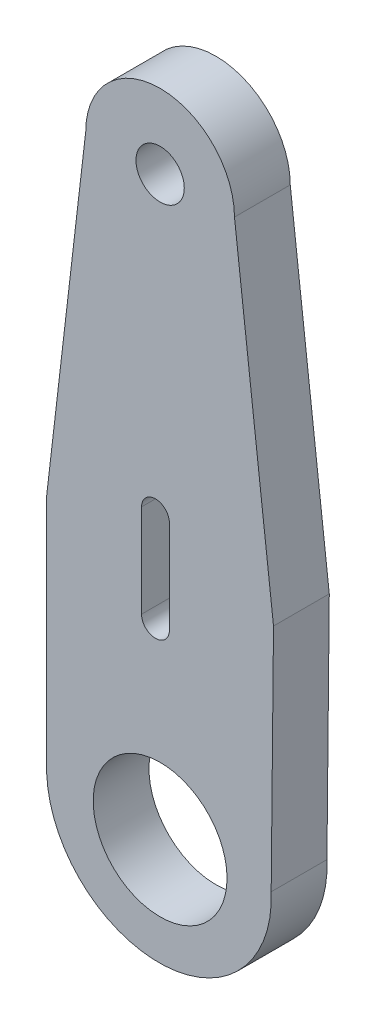
SolidWorks part; units mm, degrees
ref_plane "Front Plane" through (0, 0, 0) normal (0, 0, 1) x (1, 0, 0)
ref_plane "Top Plane" through (0, 0, 0) normal (0, 1, 0) x (1, 0, 0)
ref_plane "Right Plane" through (0, 0, 0) normal (1, 0, 0) x (0, 0, -1)
sketch "Model" plane through (0, 0, 0) normal (0, 0, 1) x (1, 0, 0)
  line L0 (54.4, 32.325) -> (54.4, 38.325)
  line L1 (66.6, 38.325) -> (66.4744, 25.8791)
  line L2 (64.5, 56.3249) -> (66.6, 38.325)
  line L3 (56.5, 56.3249) -> (54.4, 38.325)
  line L4 (59.5, 35.3249) -> (59.5, 40.3249)
  line L5 (61, 40.3249) -> (61, 35.3249)
  line L6 (54.4, 32.325) -> (54.4, 25.325)
  circle A0 centre (60.5, 56.3249) radius 1.3
  circle A1 centre (60.5001, 25.325) radius 3.6
  arc A2 (59.5, 40.3249) -> (61, 40.3249) centre (60.25, 40.3249) cw
  arc A3 (59.5, 35.3249) -> (61, 35.3249) centre (60.25, 35.3249) ccw
  arc A4 (64.5, 56.3249) -> (56.5, 56.3249) centre (60.5, 56.3249) ccw
  arc A5 (54.4, 25.325) -> (66.4744, 25.8791) centre (60.4372, 25.6021) ccw
  point P19 (61, 40.3246)
extrude "Boss-Extrude1" add sketch "Model" along normal blind 3
